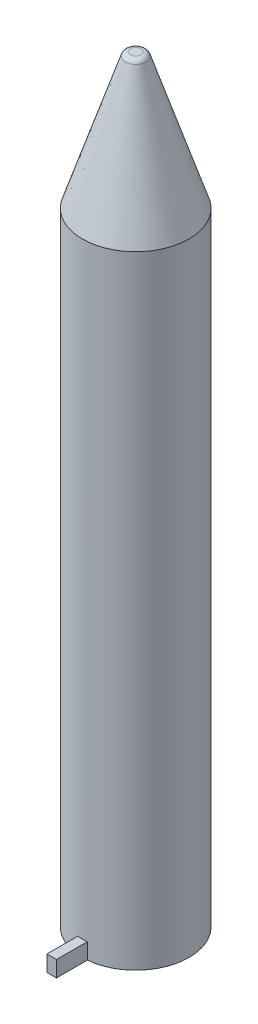
SolidWorks part; units mm, degrees
ref_plane "Front Plane" through (0, 0, 0) normal (0, 0, 1) x (1, 0, 0)
ref_plane "Top Plane" through (0, 0, 0) normal (0, 1, 0) x (1, 0, 0)
ref_plane "Right Plane" through (0, 0, 0) normal (1, 0, 0) x (0, 0, -1)
sketch "Sketch1" plane through (0, 0, 0) normal (0, 1, 0) x (1, 0, 0)
  circle A0 centre (0, 0) radius 10
  dimension "D1" = 20
extrude "Boss-Extrude1" add sketch "Sketch1" along normal blind 116.65
sketch "Sketch2" plane through (0, 0, 0) normal (0, 0, 1) x (1, 0, 0)
  line L8 (0, 116.65) -> (0, 142.05)
  line L9 (10, 116.65) -> (-10, 116.65) construction
  line L10 (1.9508, 141.3597) -> (10, 116.65)
  line L11 (10, 116.65) -> (0, 116.65)
  line L12 (1, 142.05) -> (0, 142.05)
  arc A3 (1, 142.05) -> (1.9508, 141.3597) centre (1, 141.05) cw
  dimension "D2" = 25.4
  dimension "D1" = 1
revolve "Revolve1" add sketch "Sketch2" angle 360 about L8
sketch "Sketch3" plane through (0, 0, 0) normal (0, -1, 0) x (1, 0, 0)
  line L1 (-0.9, 15.75) -> (0.9, 15.75)
  line L2 (-0.9, 15.75) -> (-0.9, 9.3548)
  line L4 (0.9, 15.75) -> (0.9, 9.3548)
  arc A0 (0.9, 9.3548) -> (-0.9, 9.3548) centre (0, 0) ccw
  dimension "D1" = 0.9
  dimension "D3" = 15.75
extrude "Boss-Extrude2" add sketch "Sketch3" against normal blind 3
sketch "Sketch4" plane through (0, 0, 0) normal (0, -1, 0) x (1, 0, 0)
  circle A0 centre (0, 0) radius 6
  dimension "D1" = 12
extrude "Cut-Extrude1" cut sketch "Sketch4" against normal blind 3
